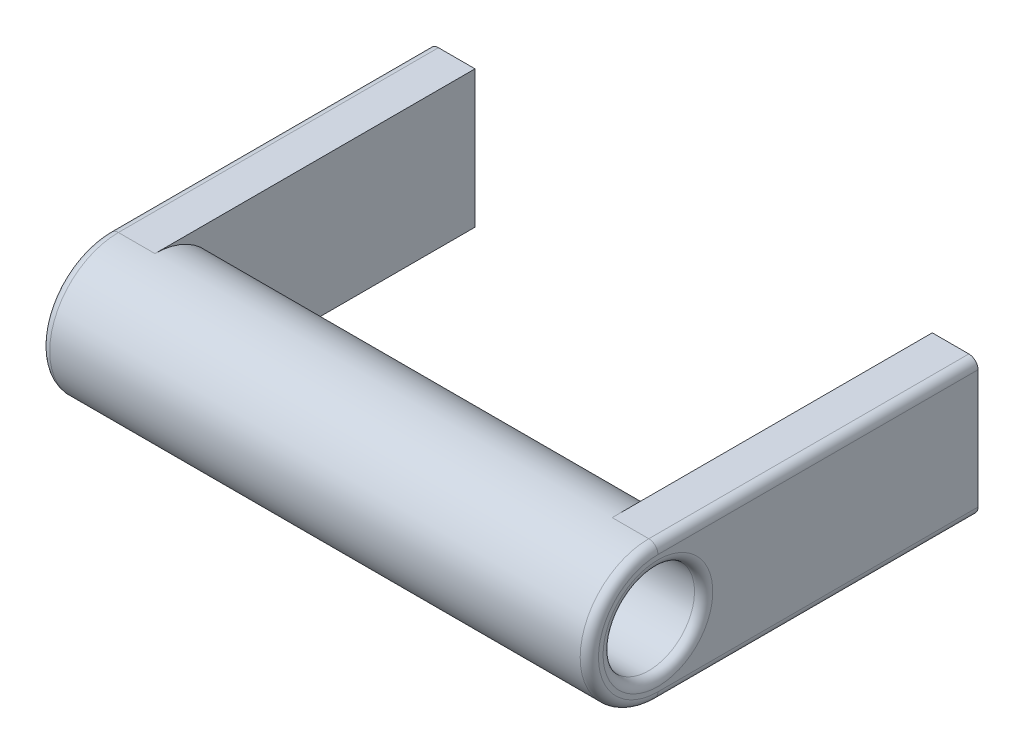
SolidWorks part; units mm, degrees
ref_plane "Спереди" through (0, 0, 0) normal (0, 0, 1) x (1, 0, 0)
ref_plane "Сверху" through (0, 0, 0) normal (0, 1, 0) x (1, 0, 0)
ref_plane "Справа" through (0, 0, 0) normal (1, 0, 0) x (0, 0, -1)
other "Configuration Table"
sketch "Sketch1" plane through (0, 0, 0) normal (0, 0, 1) x (1, 0, 0)
  line L0 (0, 0) -> (0, 51.5979) construction
  line L1 (60, -15) -> (50, -15)
  line L2 (60, -15) -> (60, 15)
  line L3 (60, 15) -> (50, 15)
  line L4 (50, -15) -> (50, 15)
  line L5 (60, -15) -> (50, 15) construction
  line L6 (60, 15) -> (50, -15) construction
  line L7 (0, 0) -> (55, 0) construction
  line L8 (-60, 15) -> (-50, 15)
  line L9 (-50, -15) -> (-50, 15)
  line L10 (-60, -15) -> (-50, -15)
  line L11 (-60, -15) -> (-60, 15)
  point P0 (55, 0)
  point P13 (-55, 15)
  dimension "D1" = 110
  dimension "D2" = 10
  dimension "D3" = 30
extrude "Boss-Extrude1" add sketch "Sketch1" along normal blind 70
sketch "Sketch2" plane through (60, 0, 0) normal (1, 0, 0) x (0, 0, -1)
  line L0 (-70, -15) -> (-70, 15) construction
  line L1 (-70, -15) -> (0, -15) construction
  circle A0 centre (-70, 0) radius 15
extrude "Boss-Extrude2" add sketch "Sketch2" against normal up to surface (120 mm away) up to face at (-60, 0, 35)
sketch "Sketch3" plane through (-60, 0, 0) normal (-1, 0, 0) x (0, 0, 1)
  line L0 (70, 15) -> (70, -15) construction
  line L1 (70, -15) -> (0, -15) construction
  arc A0 (70, -15) -> (70, 15) centre (70, 0) ccw construction
  circle A1 centre (70, 0) radius 10
  dimension "D1" = 5
extrude "Cut-Extrude1" cut sketch "Sketch3" against normal up to next and the other way through all
fillet "Fillet1" radius 2 8 edges at (-60, -15, 35) (-60, 0, 85) (60, -15, 35) (60, 0, 85) (-60, 10, 70) (-60, 15, 35) (60, 0, 80) (60, 15, 35)
sketch "Sketch4" plane through (0, 0, 0) normal (0, 0, -1) x (-1, 0, 0)
  line L0 (-50, 0) -> (-60, 0) construction
  line L1 (-50, 15) -> (-50, -15) construction
  line L2 (-60, -13) -> (-60, 13) construction
  line L3 (-55, 0) -> (-55, 12.211) construction
  line L4 (0, 0) -> (0, 44.7084) construction
  circle A0 centre (-55, 7) radius 1.5
  circle A1 centre (-55, -7) radius 1.5
  circle A2 centre (55, -7) radius 1.5
  circle A3 centre (55, 7) radius 1.5
  dimension "D1" = 3
  dimension "D2" = 14
extrude "Cut-Extrude2" cut sketch "Sketch4" against normal blind 15
